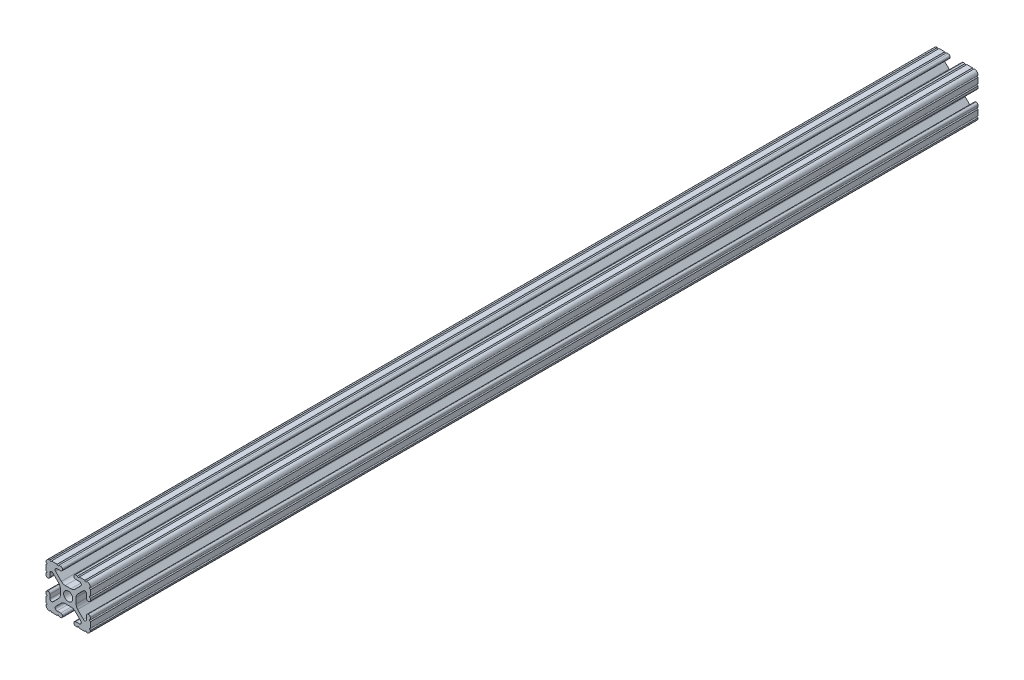
SolidWorks part; units mm, degrees
ref_plane "Front Plane" through (0, 0, 0) normal (0, 0, 1) x (1, 0, 0)
ref_plane "Top Plane" through (0, 0, 0) normal (0, 1, 0) x (1, 0, 0)
ref_plane "Right Plane" through (0, 0, 0) normal (1, 0, 0) x (0, 0, -1)
sketch "Sketch1" plane through (0, 0, 0) normal (0, 0, 1) x (1, 0, 0)
  line L0 (-7.207, 8.7244) -> (-3.8983, 5.4232)
  line L1 (-4.2875, 10.4902) -> (-6.4768, 10.4902)
  line L2 (-3.2385, 11.651) -> (-3.2385, 11.5392)
  line L3 (-5.3171, 12.7) -> (-4.2875, 12.7)
  line L4 (0, 13.4005) -> (0, -14.8534) construction
  line L5 (12.7, 0) -> (-13.9989, 0) construction
  line L6 (-9.5504, 12.7) -> (-6.3331, 12.7)
  line L7 (-12.7, 6.3331) -> (-12.7, 9.5504)
  line L8 (-12.7, 4.2875) -> (-12.7, 5.3171)
  line L9 (-11.5392, 3.2385) -> (-11.651, 3.2385)
  line L10 (-10.4902, 6.4021) -> (-10.4902, 4.2875)
  line L11 (-5.441, 3.8408) -> (-8.7371, 7.1294)
  line L12 (-4.5085, -1.5932) -> (-4.5085, 1.5932)
  line L13 (-1.7093, -4.4958) -> (1.7093, -4.4958)
  line L14 (3.9523, -5.4237) -> (7.1797, -8.6452)
  line L15 (6.4164, -10.4902) -> (4.2875, -10.4902)
  line L16 (3.2385, -11.5392) -> (3.2385, -11.651)
  line L17 (4.2875, -12.7) -> (5.3171, -12.7)
  line L18 (6.3331, -12.7) -> (9.5504, -12.7)
  line L19 (12.7, -9.5504) -> (12.7, -6.3331)
  line L20 (12.7, -5.3171) -> (12.7, -4.2875)
  line L21 (11.651, -3.2385) -> (11.5392, -3.2385)
  line L22 (10.4902, -4.2875) -> (10.4902, -6.4021)
  line L23 (8.7371, -7.1294) -> (5.441, -3.8408)
  line L24 (4.5085, -1.5932) -> (4.5085, 1.5932)
  line L25 (5.441, 3.8408) -> (8.7371, 7.1294)
  line L26 (10.4902, 6.4021) -> (10.4902, 4.2875)
  line L27 (11.5392, 3.2385) -> (11.651, 3.2385)
  line L28 (12.7, 4.2875) -> (12.7, 5.3171)
  line L29 (12.7, 6.3331) -> (12.7, 9.5504)
  line L30 (9.5504, 12.7) -> (6.3331, 12.7)
  line L31 (5.3171, 12.7) -> (4.2875, 12.7)
  line L32 (3.2385, 11.651) -> (3.2385, 11.5392)
  line L33 (4.2875, 10.4902) -> (6.4768, 10.4902)
  line L34 (7.207, 8.7244) -> (3.8983, 5.4232)
  line L35 (1.6558, 4.4958) -> (-1.6558, 4.4958)
  line L36 (-8.7371, -7.1294) -> (-5.441, -3.8408)
  line L37 (-10.4902, -4.2875) -> (-10.4902, -6.4021)
  line L38 (-11.651, -3.2385) -> (-11.5392, -3.2385)
  line L39 (-12.7, -5.3171) -> (-12.7, -4.2875)
  line L40 (-12.7, -9.5504) -> (-12.7, -6.3331)
  line L41 (-6.3331, -12.7) -> (-9.5504, -12.7)
  line L42 (-4.2875, -12.7) -> (-5.3171, -12.7)
  line L43 (-3.2385, -11.5392) -> (-3.2385, -11.651)
  line L44 (-6.4164, -10.4902) -> (-4.2875, -10.4902)
  line L45 (-3.9523, -5.4237) -> (-7.1797, -8.6452)
  arc A0 (-7.207, 8.7244) -> (-6.4768, 10.4902) centre (-6.4768, 9.4563) cw
  arc A1 (-3.2385, 11.5392) -> (-4.2875, 10.4902) centre (-4.2875, 11.5392) cw
  arc A2 (-4.2875, 12.7) -> (-3.2385, 11.651) centre (-4.2875, 11.651) cw
  arc A3 (-5.3171, 12.7) -> (-6.3331, 12.7) centre (-5.8251, 12.7) cw
  arc A4 (-9.5504, 12.7) -> (-10.5664, 12.6998) centre (-10.0584, 12.7) cw
  arc A5 (-12.6998, 10.5664) -> (-10.5664, 12.6998) centre (-10.5918, 10.5918) cw
  arc A6 (-12.6998, 10.5664) -> (-12.7, 9.5504) centre (-12.7, 10.0584) cw
  arc A7 (-12.7, 6.3331) -> (-12.7, 5.3171) centre (-12.7, 5.8251) cw
  arc A8 (-11.651, 3.2385) -> (-12.7, 4.2875) centre (-11.651, 4.2875) cw
  arc A9 (-10.4902, 4.2875) -> (-11.5392, 3.2385) centre (-11.5392, 4.2875) cw
  circle A10 centre (0, 0) radius 2.6035
  arc A11 (-10.4902, 6.4021) -> (-8.7371, 7.1294) centre (-9.4628, 6.4021) cw
  arc A12 (-5.441, 3.8408) -> (-4.5085, 1.5932) centre (-7.6835, 1.5932) cw
  arc A13 (-4.5085, -1.5932) -> (-5.441, -3.8408) centre (-7.6835, -1.5932) cw
  arc A14 (-8.7371, -7.1294) -> (-10.4902, -6.4021) centre (-9.4628, -6.4021) cw
  arc A15 (-1.7093, -4.4958) -> (-3.9523, -5.4237) centre (-1.7093, -7.6708) ccw
  arc A16 (3.9523, -5.4237) -> (1.7093, -4.4958) centre (1.7093, -7.6708) ccw
  arc A17 (6.4164, -10.4902) -> (7.1797, -8.6452) centre (6.4164, -9.4098) ccw
  arc A18 (4.2875, -10.4902) -> (3.2385, -11.5392) centre (4.2875, -11.5392) ccw
  arc A19 (3.2385, -11.651) -> (4.2875, -12.7) centre (4.2875, -11.651) ccw
  arc A20 (6.3331, -12.7) -> (5.3171, -12.7) centre (5.8251, -12.7) ccw
  arc A21 (10.5664, -12.6998) -> (9.5504, -12.7) centre (10.0584, -12.7) ccw
  arc A22 (10.5664, -12.6998) -> (12.6998, -10.5664) centre (10.5918, -10.5918) ccw
  arc A23 (12.7, -9.5504) -> (12.6998, -10.5664) centre (12.7, -10.0584) ccw
  arc A24 (12.7, -5.3171) -> (12.7, -6.3331) centre (12.7, -5.8251) ccw
  arc A25 (12.7, -4.2875) -> (11.651, -3.2385) centre (11.651, -4.2875) ccw
  arc A26 (11.5392, -3.2385) -> (10.4902, -4.2875) centre (11.5392, -4.2875) ccw
  arc A27 (8.7371, -7.1294) -> (10.4902, -6.4021) centre (9.4628, -6.4021) ccw
  arc A28 (4.5085, -1.5932) -> (5.441, -3.8408) centre (7.6835, -1.5932) ccw
  arc A29 (5.441, 3.8408) -> (4.5085, 1.5932) centre (7.6835, 1.5932) ccw
  arc A30 (10.4902, 6.4021) -> (8.7371, 7.1294) centre (9.4628, 6.4021) ccw
  arc A31 (10.4902, 4.2875) -> (11.5392, 3.2385) centre (11.5392, 4.2875) ccw
  arc A32 (11.651, 3.2385) -> (12.7, 4.2875) centre (11.651, 4.2875) ccw
  arc A33 (12.7, 6.3331) -> (12.7, 5.3171) centre (12.7, 5.8251) ccw
  arc A34 (12.6998, 10.5664) -> (12.7, 9.5504) centre (12.7, 10.0584) ccw
  arc A35 (12.6998, 10.5664) -> (10.5664, 12.6998) centre (10.5918, 10.5918) ccw
  arc A36 (9.5504, 12.7) -> (10.5664, 12.6998) centre (10.0584, 12.7) ccw
  arc A37 (5.3171, 12.7) -> (6.3331, 12.7) centre (5.8251, 12.7) ccw
  arc A38 (4.2875, 12.7) -> (3.2385, 11.651) centre (4.2875, 11.651) ccw
  arc A39 (3.2385, 11.5392) -> (4.2875, 10.4902) centre (4.2875, 11.5392) ccw
  arc A40 (7.207, 8.7244) -> (6.4768, 10.4902) centre (6.4768, 9.4563) ccw
  arc A41 (1.6558, 4.4958) -> (3.8983, 5.4232) centre (1.6558, 7.6708) ccw
  arc A42 (-1.6558, 4.4958) -> (-3.8983, 5.4232) centre (-1.6558, 7.6708) cw
  arc A43 (-11.5392, -3.2385) -> (-10.4902, -4.2875) centre (-11.5392, -4.2875) cw
  arc A44 (-12.7, -4.2875) -> (-11.651, -3.2385) centre (-11.651, -4.2875) cw
  arc A45 (-12.7, -5.3171) -> (-12.7, -6.3331) centre (-12.7, -5.8251) cw
  arc A46 (-12.7, -9.5504) -> (-12.6998, -10.5664) centre (-12.7, -10.0584) cw
  arc A47 (-10.5664, -12.6998) -> (-12.6998, -10.5664) centre (-10.5918, -10.5918) cw
  arc A48 (-10.5664, -12.6998) -> (-9.5504, -12.7) centre (-10.0584, -12.7) cw
  arc A49 (-6.3331, -12.7) -> (-5.3171, -12.7) centre (-5.8251, -12.7) cw
  arc A50 (-3.2385, -11.651) -> (-4.2875, -12.7) centre (-4.2875, -11.651) cw
  arc A51 (-4.2875, -10.4902) -> (-3.2385, -11.5392) centre (-4.2875, -11.5392) cw
  arc A52 (-6.4164, -10.4902) -> (-7.1797, -8.6452) centre (-6.4164, -9.4098) cw
  dimension "D1" = 5.207
  dimension "D9" = 14.859
  dimension "D2" = 25.4
  dimension "D3" = 12.7
  dimension "D4" = 6.477
  dimension "D5" = 8.2042
  dimension "D6" = 9.017
  dimension "D8" = 2.2098
  dimension "D10" = 2.2098
extrude "Extrude1" add sketch "Sketch1" against normal blind 508
